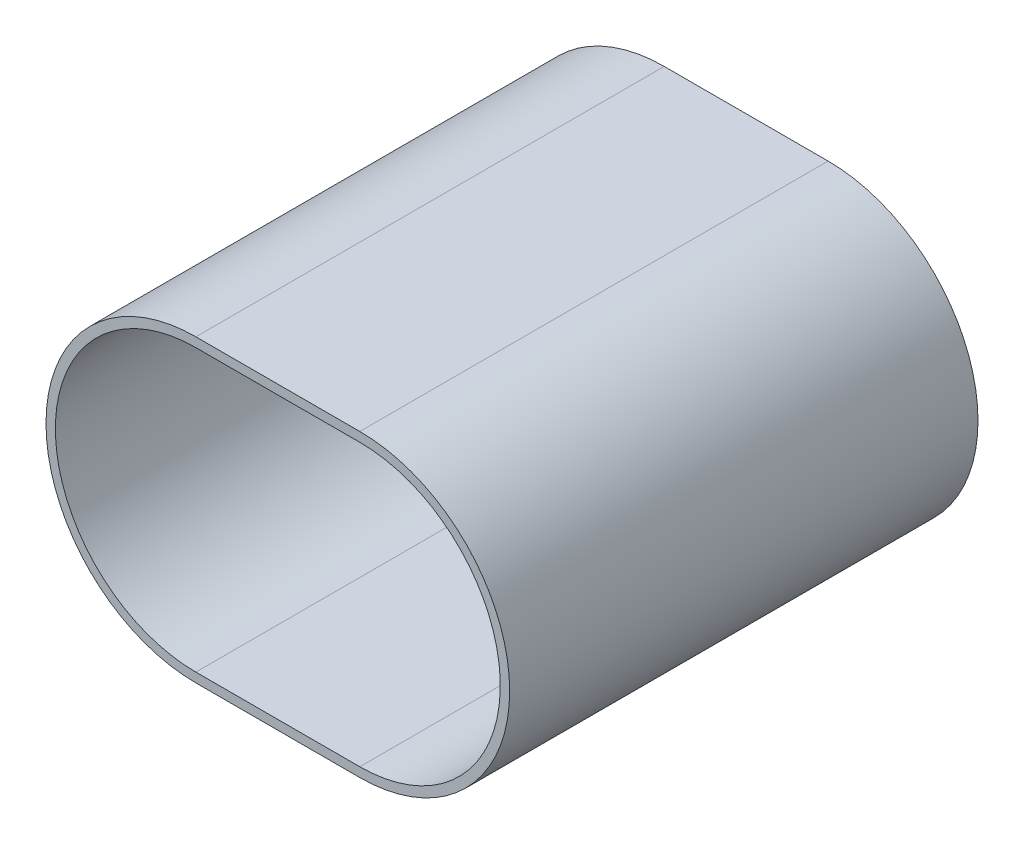
SolidWorks part; units mm, degrees
ref_plane "Front Plane" through (0, 0, 0) normal (0, 0, 1) x (1, 0, 0)
ref_plane "Top Plane" through (0, 0, 0) normal (0, 1, 0) x (1, 0, 0)
ref_plane "Right Plane" through (0, 0, 0) normal (1, 0, 0) x (0, 0, -1)
sketch "Sketch1" plane through (0, 0, 0) normal (0, 0, 1) x (1, 0, 0)
  line L0 (0, 0) -> (35, 0) construction
  line L1 (0, 32) -> (35, 32)
  line L2 (0, 30) -> (35, 30)
  line L3 (0, -30) -> (35, -30)
  line L4 (0, -32) -> (35, -32)
  arc A0 (0, 30) -> (0, -30) centre (0, 0) ccw
  arc A1 (35, -30) -> (35, 30) centre (35, 0) ccw
  arc A2 (35, -32) -> (35, 32) centre (35, 0) ccw
  arc A3 (0, 32) -> (0, -32) centre (0, 0) ccw
  point P5 (17.5, 0)
  dimension "D1" = 30
  dimension "D3" = 35
  dimension "D2" = 2
extrude "Boss-Extrude1" add sketch "Sketch1" along normal blind 100
